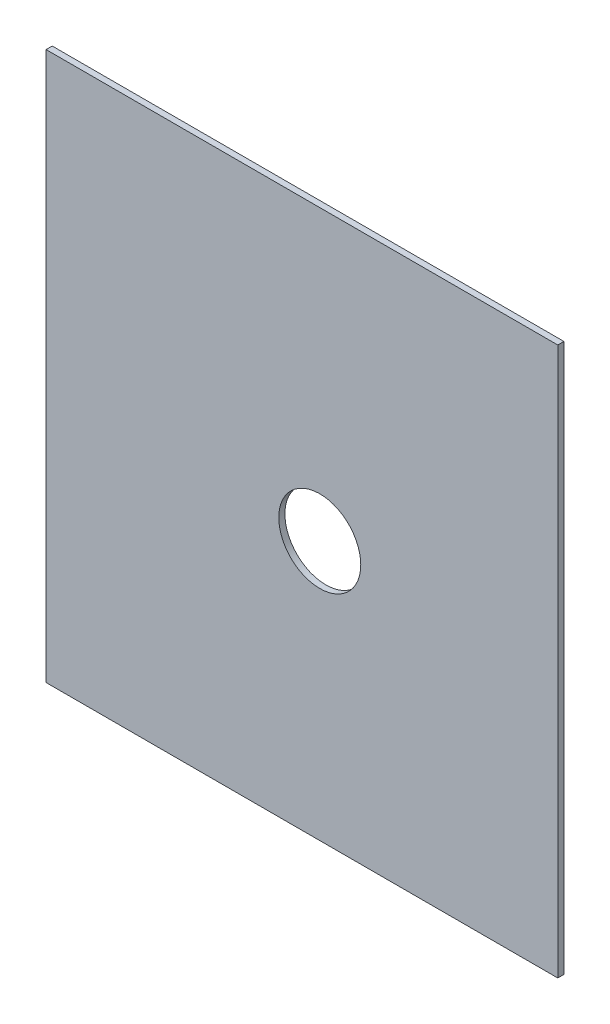
SolidWorks part; units mm, degrees
ref_plane "Front Plane" through (0, 0, 0) normal (0, 0, 1) x (1, 0, 0)
ref_plane "Top Plane" through (0, 0, 0) normal (0, 1, 0) x (1, 0, 0)
ref_plane "Right Plane" through (0, 0, 0) normal (1, 0, 0) x (0, 0, -1)
sketch "Sketch1" plane through (0, 0, 0) normal (0, 0, 1) x (1, 0, 0)
  line L0 (71, -267.4) -> (0, -267.4) construction
  line L1 (0, 0) -> (249.6, 0)
  line L2 (0, 0) -> (0, -267.4)
  line L3 (0, -267.4) -> (249.6, -267.4)
  line L4 (249.6, 0) -> (249.6, -267.4)
  dimension "D2" = 249.6
extrude "Boss-Extrude1" add sketch "Sketch1" along normal blind 3
sketch "Sketch2" plane through (0, 0, 3) normal (0, 0, 1) x (1, 0, 0)
  line L0 (133.5, 0) -> (133.5, -350.4) construction
  circle A0 centre (133.5, -140.911) radius 20
  dimension "D1" = 40
extrude "Cut-Extrude1" cut sketch "Sketch2" against normal through all
